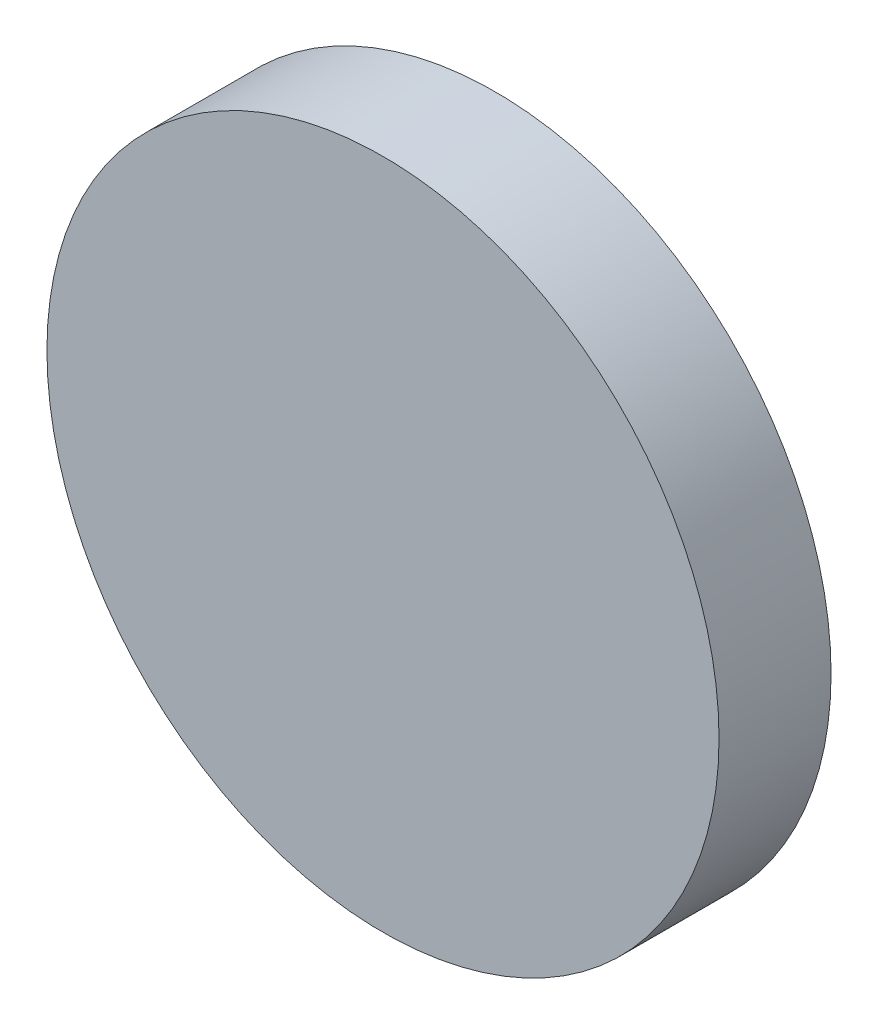
SolidWorks part; units mm, degrees
material "Vetro"
ref_plane "Front Plane" through (0, 0, 0) normal (0, 0, 1) x (1, 0, 0)
ref_plane "Top Plane" through (0, 0, 0) normal (0, 1, 0) x (1, 0, 0)
ref_plane "Right Plane" through (0, 0, 0) normal (1, 0, 0) x (0, 0, -1)
sketch "Schizzo1" plane through (0, 0, 0) normal (0, 0, 1) x (1, 0, 0)
  circle A0 centre (0, 0) radius 6
  dimension "D1" = 12
extrude "Estrusione-Estrusione1" add sketch "Schizzo1" along normal blind 2
